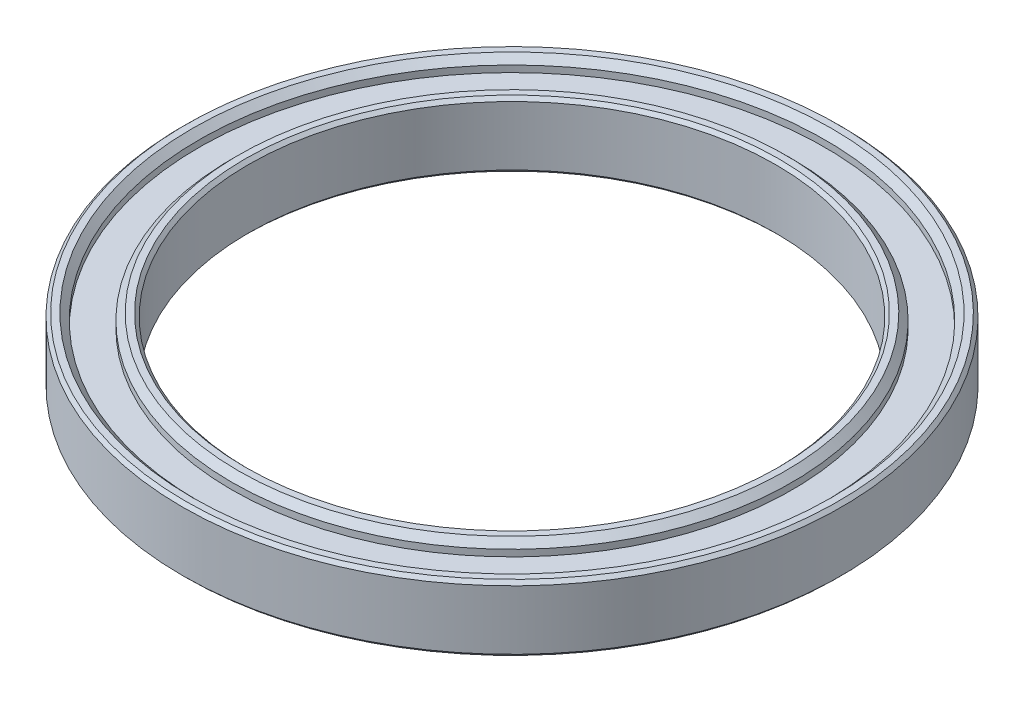
SolidWorks part; units mm, degrees
ref_plane "Front Plane" through (0, 0, 0) normal (0, 0, 1) x (1, 0, 0)
ref_plane "Top Plane" through (0, 0, 0) normal (0, 1, 0) x (1, 0, 0)
ref_plane "Right Plane" through (0, 0, 0) normal (1, 0, 0) x (0, 0, -1)
sketch "Sketch1" plane through (0, 0, 0) normal (0, 1, 0) x (1, 0, 0)
  circle A0 centre (0, 0) radius 50
  circle A1 centre (0, 0) radius 40
  dimension "D1" = 100
  dimension "D2" = 80
extrude "Boss-Extrude1" add sketch "Sketch1" along normal blind 10
chamfer "Chamfer1" distance 0.5 angle 45 4 edges at (0, 0, 40) (0, 0, 50) (0, 10, 50) (0, 10, 40)
sketch "Sketch2" plane through (0, 10, 0) normal (0, 1, 0) x (1, 0, 0)
  circle A0 centre (0, 0) radius 42.5
  circle A1 centre (0, 0) radius 47.5
  dimension "D1" = 85
  dimension "D2" = 95
extrude "Cut-Extrude1" cut sketch "Sketch2" against normal blind 2
chamfer "Chamfer2" distance 1 angle 45 2 edges at (0, 10, 47.5) (0, 10, 42.5)
sketch "Sketch3" plane through (0, 0, 0) normal (0, -1, 0) x (1, 0, 0)
  circle A0 centre (0, 0) radius 47.5
  circle A1 centre (0, 0) radius 42.5
  dimension "D1" = 95
  dimension "D2" = 85
extrude "Cut-Extrude2" cut sketch "Sketch3" against normal blind 2
chamfer "Chamfer3" distance 1 angle 45 2 edges at (0, 0, -42.5) (0, 0, -47.5)
